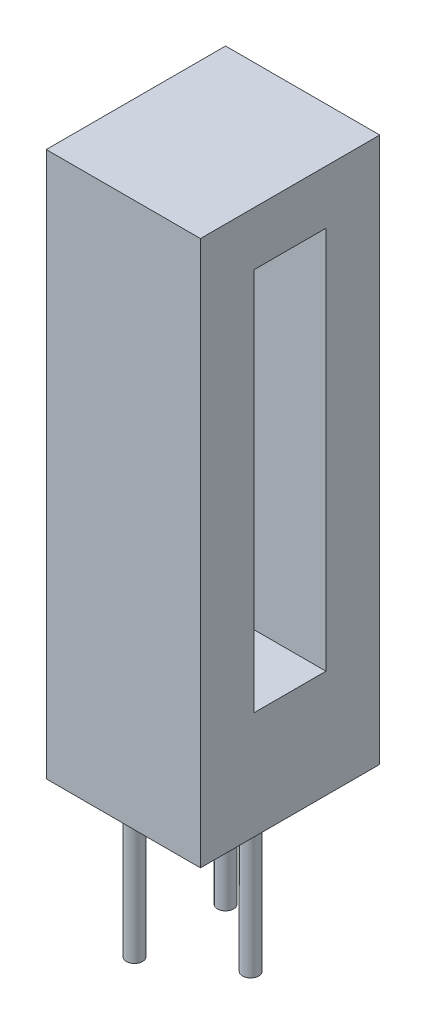
SolidWorks part; units mm, degrees
ref_plane "Front Plane" through (0, 0, 0) normal (0, 0, 1) x (1, 0, 0)
ref_plane "Top Plane" through (0, 0, 0) normal (0, 1, 0) x (1, 0, 0)
ref_plane "Right Plane" through (0, 0, 0) normal (1, 0, 0) x (0, 0, -1)
sketch "Sketch1" plane through (0, 0, 0) normal (0, 0, 1) x (1, 0, 0)
  line L0 (0, 0) -> (4.3, 0)
  line L1 (4.3, 0) -> (4.3, 15.2)
  line L2 (4.3, 15.2) -> (0, 15.2)
  line L3 (0, 15.2) -> (0, 0)
  dimension "D1" = 4.3
  dimension "D2" = 15.2
extrude "Boss-Extrude1" add sketch "Sketch1" against normal blind 5
sketch "Sketch2" plane through (4.3, 0, 0) normal (1, 0, 0) x (0, 0, -1)
  line L0 (1.5, 3) -> (1.5, 13.7)
  line L2 (1.5, 13.7) -> (3.5, 13.7)
  line L3 (3.5, 13.7) -> (3.5, 3)
  line L4 (0, 0) -> (0, 15.2) construction
  line L5 (5, 0) -> (5, 15.2) construction
  line L6 (5, 15.2) -> (0, 15.2) construction
  line L7 (3.5, 3) -> (1.5, 3)
  line L8 (5, 0) -> (0, 0) construction
  dimension "D1" = 1.5
  dimension "D2" = 1.5
  dimension "D3" = 1.5
  dimension "D4" = 3
extrude "Cut-Extrude1" cut sketch "Sketch2" against normal blind 2
sketch "Sketch3" plane through (0, 0, 0) normal (0, -1, 0) x (1, 0, 0)
  line L0 (0, -2.5) -> (4.3, -2.5) construction
  line L1 (0, -5) -> (0, 0) construction
  line L2 (0, 0) -> (4.3, 0) construction
  circle A0 centre (1.23, -1.23) radius 0.225
  circle A1 centre (1.23, -3.77) radius 0.225
  circle A2 centre (3.2, -2.5) radius 0.225
  dimension "D1" = 0.45
  dimension "D4" = 0.45
  dimension "D2" = 1.23
  dimension "D3" = 1.23
  dimension "D5" = 3.2
extrude "Boss-Extrude2" add sketch "Sketch3" along normal blind 4.3
